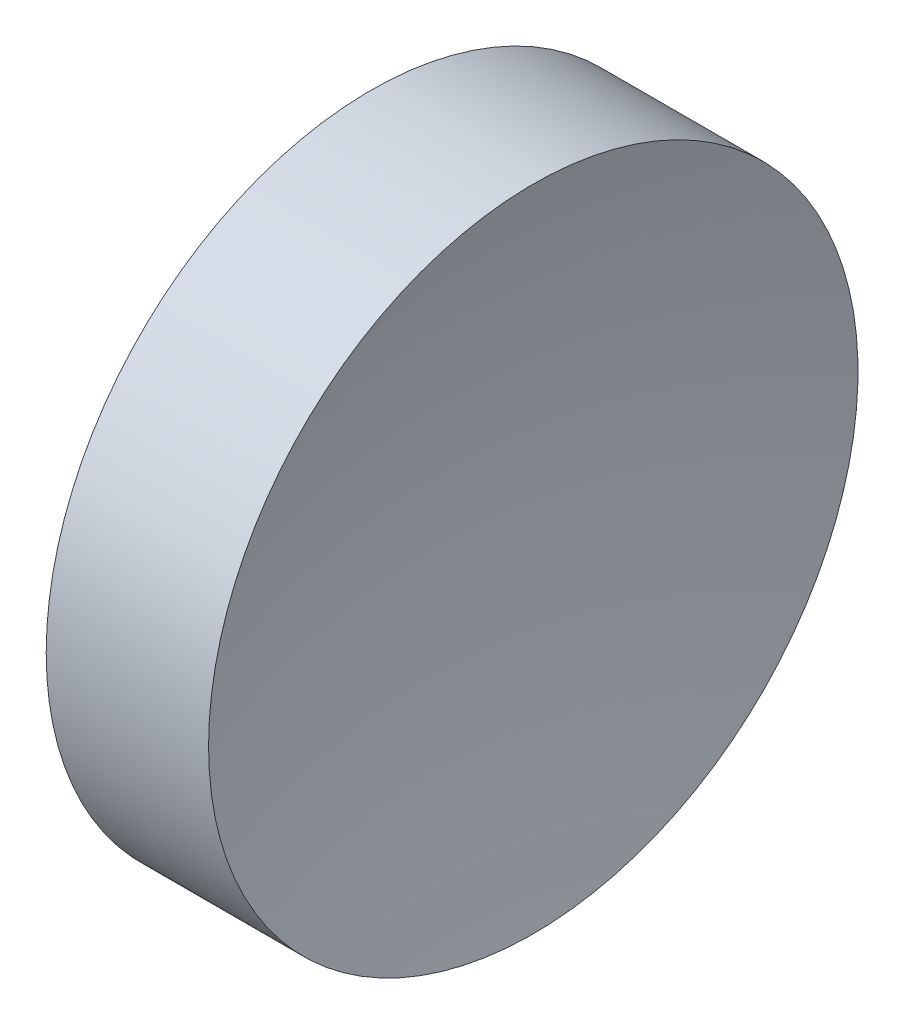
SolidWorks part; units mm, degrees
ref_plane "前视基准面" through (0, 0, 0) normal (0, 0, 1) x (1, 0, 0)
ref_plane "上视基准面" through (0, 0, 0) normal (0, 1, 0) x (1, 0, 0)
ref_plane "右视基准面" through (0, 0, 0) normal (1, 0, 0) x (0, 0, -1)
sketch "草图1" plane through (0, 0, 0) normal (0, 1, 0) x (1, 0, 0)
  line L0 (0, 0) -> (6.9328, 0) construction
  line L1 (0, 0) -> (4.71, 0)
  line L2 (0, 0) -> (0, 12.7)
  line L3 (0, 12.7) -> (6.3498, 12.7)
  arc A0 (6.3498, 12.7) -> (4.71, 0) centre (54.71, 0) ccw
  dimension "D3" = 50
  dimension "D1" = 4.71
  dimension "D2" = 12.7
revolve "旋转1" add sketch "草图1" angle 360 about L0
